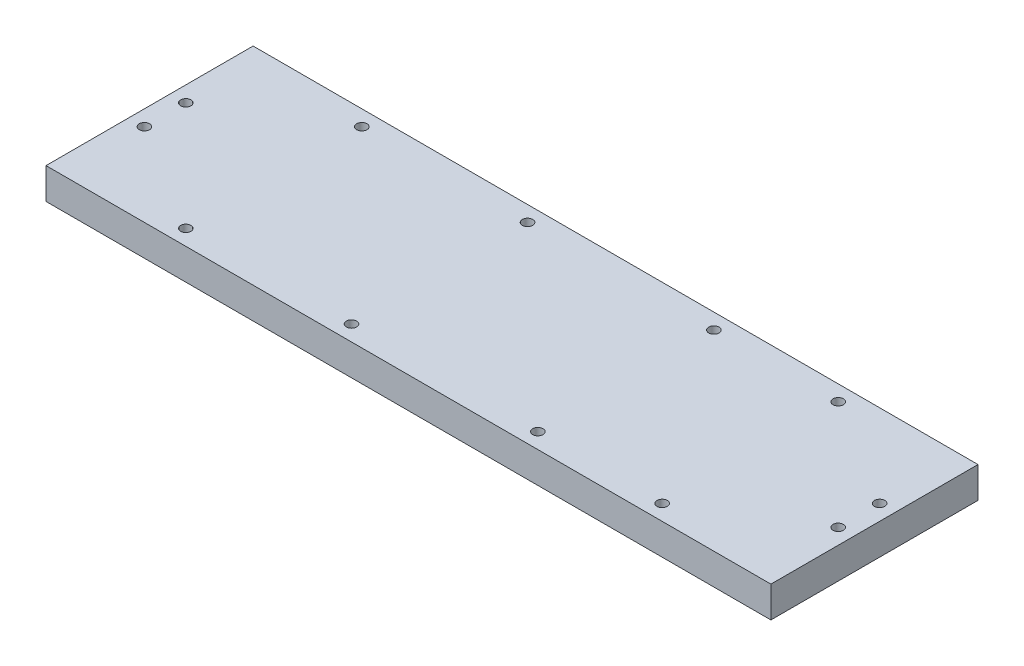
SolidWorks part; units mm, degrees
material "Oak"
ref_plane "Front Plane" through (0, 0, 0) normal (0, 0, 1) x (1, 0, 0)
ref_plane "Top Plane" through (0, 0, 0) normal (0, 1, 0) x (1, 0, 0)
ref_plane "Right Plane" through (0, 0, 0) normal (1, 0, 0) x (0, 0, -1)
other "Configuration Table"
sketch "Sketch1" plane through (0, 0, 0) normal (0, 1, 0) x (1, 0, 0)
  line L1 (-222.25, 63.5) -> (222.25, 63.5)
  line L2 (-222.25, 63.5) -> (-222.25, -63.5)
  line L3 (-222.25, -63.5) -> (222.25, -63.5)
  line L4 (222.25, 63.5) -> (222.25, -63.5)
  line L5 (-222.25, 63.5) -> (222.25, -63.5) construction
  line L6 (-222.25, -63.5) -> (222.25, 63.5) construction
  point P0 (0, 0)
  dimension "D1" = 127
  dimension "D2" = 444.5
extrude "Boss-Extrude1" add sketch "Sketch1" along normal blind 19.05
sketch "Sketch2" plane through (0, 19.05, 0) normal (0, 1, 0) x (1, 0, 0)
  line L0 (-232.7429, 0) -> (247.9108, 0) construction
  line L1 (-222.25, 63.5) -> (-222.25, -63.5) construction
  line L2 (222.25, -63.5) -> (222.25, 63.5) construction
  line L3 (-222.25, -63.5) -> (222.25, -63.5) construction
  circle A0 centre (-146.05, -53.975) radius 3.175
  circle A1 centre (-44.45, -53.975) radius 3.175
  circle A2 centre (69.85, -53.975) radius 3.175
  circle A3 centre (146.05, -53.975) radius 3.175
  dimension "D6" = 6.35
  dimension "D1" = 76.2
  dimension "D2" = 101.6
  dimension "D3" = 114.3
  dimension "D4" = 76.2
  dimension "D5" = 76.2
  dimension "D7" = 9.525
  dimension "D8" = 9.525
  dimension "D9" = 9.525
extrude "Cut-Extrude1" cut sketch "Sketch2" against normal blind 12.7
mirror "Mirror1" about plane through (0, 0, 0) normal (0, 0, 1) of "Cut-Extrude1"
sketch "Sketch3" plane through (0, 19.05, 0) normal (0, 1, 0) x (1, 0, 0)
  line L0 (222.25, 63.5) -> (-222.25, 63.5) construction
  line L2 (-222.25, 63.5) -> (-222.25, -63.5) construction
  line L3 (-233.6565, 44.45) -> (250.0827, 44.45) construction
  line L4 (-222.25, -63.5) -> (222.25, -63.5) construction
  circle A0 centre (-212.725, 12.7) radius 3.175
  circle A1 centre (-212.725, -12.7) radius 3.175
  dimension "D2" = 6.35
  dimension "D4" = 6.35
  dimension "D1" = 31.75
  dimension "D3" = 50.8
  dimension "D5" = 9.525
  dimension "D6" = 9.525
  dimension "D7" = 19.05
extrude "Cut-Extrude2" cut sketch "Sketch3" against normal blind 12.7
mirror "Mirror3" about plane through (0, 0, 0) normal (1, 0, 0) of "Cut-Extrude2"
sketch "Sketch4" plane through (0, 0, 0) normal (0, -1, 0) x (1, 0, 0)
  line L0 (-238.3649, 0) -> (238.9315, 0) construction
  line L1 (-222.25, -63.5) -> (-222.25, 63.5) construction
  line L2 (222.25, 63.5) -> (222.25, -63.5) construction
  circle A0 centre (-95.25, -31.75) radius 1.5875
  circle A1 centre (0, -31.75) radius 1.5875
  circle A2 centre (95.25, -31.75) radius 1.5875
  dimension "D5" = 3.175
  dimension "D1" = 127
  dimension "D2" = 127
  dimension "D3" = 95.25
  dimension "D4" = 31.75
extrude "Cut-Extrude3" cut sketch "Sketch4" against normal blind 6.35
mirror "Mirror4" about plane through (0, 0, 0) normal (0, 0, 1) of "Cut-Extrude3"
